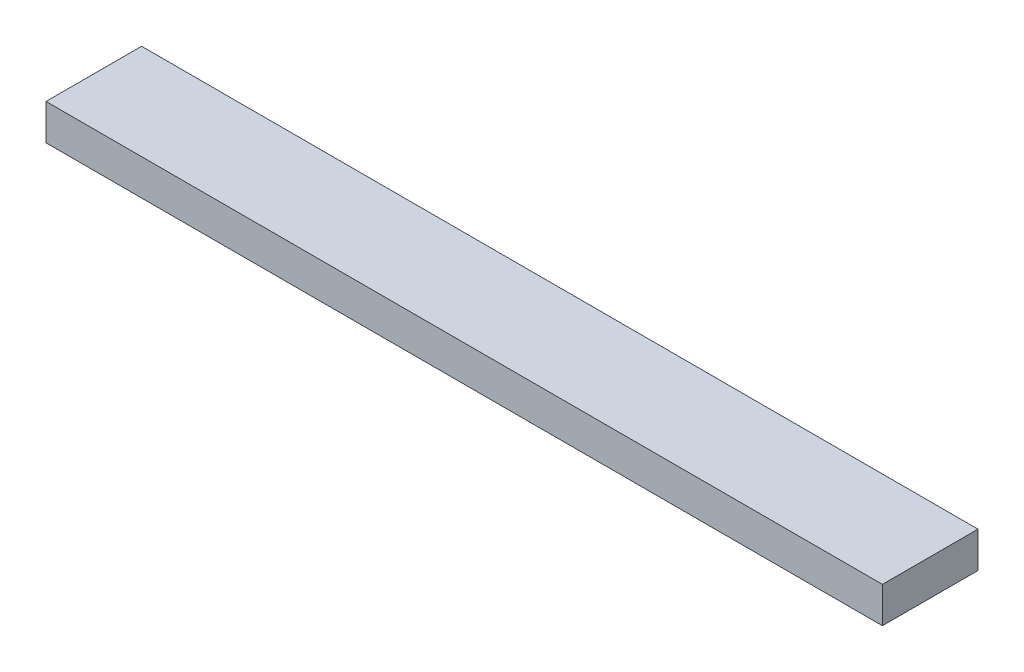
SolidWorks part; units mm, degrees
ref_plane "Ön Düzlem" through (0, 0, 0) normal (0, 0, 1) x (1, 0, 0)
ref_plane "Üst Düzlem" through (0, 0, 0) normal (0, 1, 0) x (1, 0, 0)
ref_plane "Sağ Düzlem" through (0, 0, 0) normal (1, 0, 0) x (0, 0, -1)
sketch "Çizim1" plane through (0, 0, 0) normal (0, 1, 0) x (1, 0, 0)
  line L1 (-350, -40) -> (350, -40)
  line L2 (-350, -40) -> (-350, 40)
  line L3 (-350, 40) -> (350, 40)
  line L4 (350, -40) -> (350, 40)
  line L5 (-350, -40) -> (350, 40) construction
  line L6 (-350, 40) -> (350, -40) construction
  point P0 (0, 0)
  dimension "D1" = 80
  dimension "D2" = 700
extrude "Yükseklik-Ekstrüzyon1" add sketch "Çizim1" against normal blind 30
